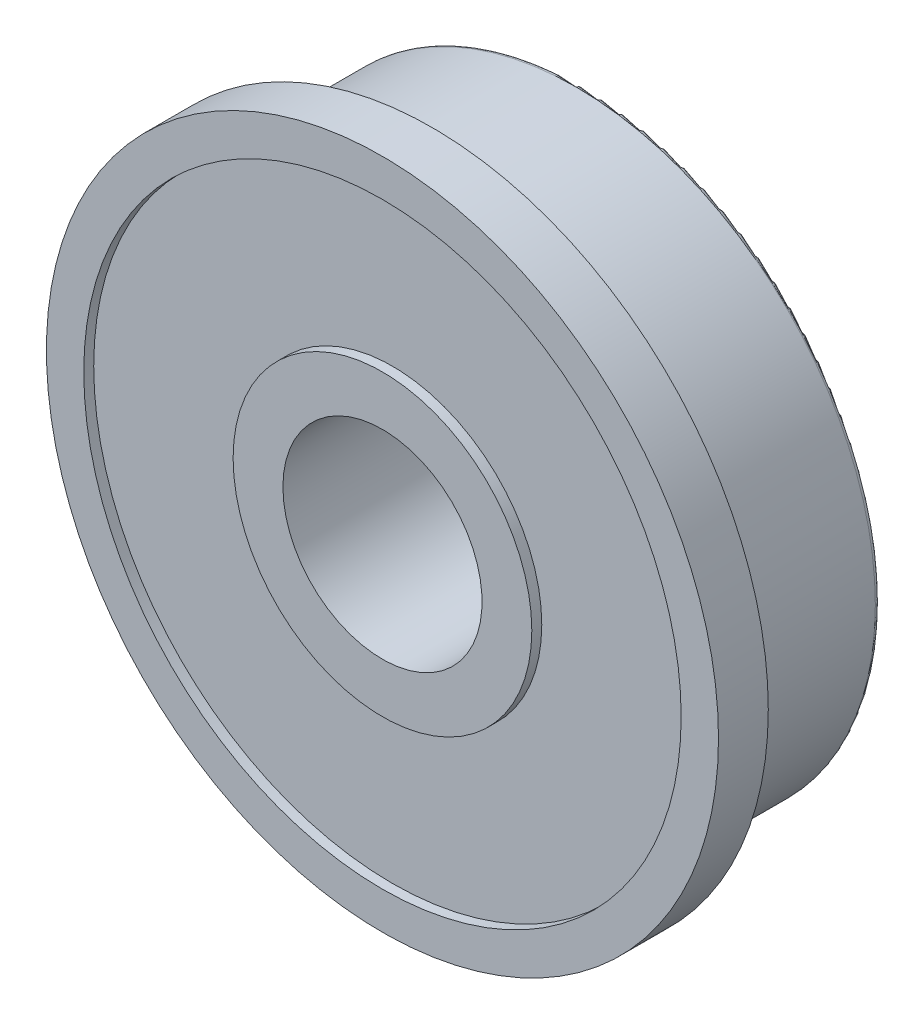
SolidWorks part; units mm, degrees
ref_plane "前基準面" through (0, 0, 0) normal (0, 0, 1) x (1, 0, 0)
ref_plane "上基準面" through (0, 0, 0) normal (0, 1, 0) x (1, 0, 0)
ref_plane "右基準面" through (0, 0, 0) normal (1, 0, 0) x (0, 0, -1)
sketch "草圖1" plane through (0, 0, 0) normal (0, 0, 1) x (1, 0, 0)
  circle A0 centre (0, 0) radius 6
  dimension "D1" = 12
extrude "填料-伸長1" add sketch "草圖1" along normal blind 4
sketch "草圖2" plane through (0, 0, 4) normal (0, 0, 1) x (1, 0, 0)
  circle A0 centre (0, 0) radius 6.75
  dimension "D1" = 13.5
extrude "填料-伸長2" add sketch "草圖2" against normal blind 1
sketch "草圖3" plane through (0, 0, 0) normal (0, 0, -1) x (-1, 0, 0)
  circle A0 centre (0, 0) radius 2
  dimension "D1" = 4
extrude "除料-伸長1" cut sketch "草圖3" against normal through all
sketch "草圖4" plane through (0, 0, 0) normal (0, 0, -1) x (-1, 0, 0)
  circle A0 centre (0, 0) radius 5
  circle A1 centre (0, 0) radius 3
  circle A2 centre (0, 0) radius 6 construction
  circle A3 centre (0, 0) radius 2 construction
  dimension "D1" = 1
  dimension "D2" = 1
extrude "除料-伸長2" cut sketch "草圖4" against normal blind 0.2
sketch "草圖5" plane through (0, 0, 4) normal (0, 0, 1) x (1, 0, 0)
  circle A0 centre (0, 0) radius 3
  circle A1 centre (0, 0) radius 6
  circle A2 centre (0, 0) radius 2 construction
  dimension "D1" = 1
  dimension "D2" = 3
extrude "除料-伸長3" cut sketch "草圖5" against normal blind 0.2
fillet "圓角1" radius 0.1 1 edges at (6, 0, 0)
